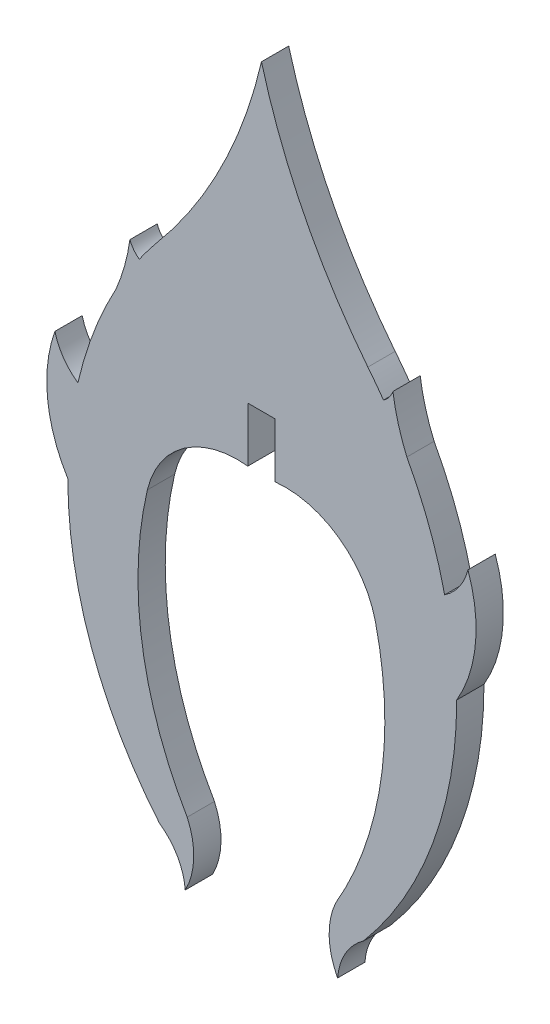
SolidWorks part; units mm, degrees
ref_plane "Front Plane" through (0, 0, 0) normal (0, 0, 1) x (1, 0, 0)
ref_plane "Top Plane" through (0, 0, 0) normal (0, 1, 0) x (1, 0, 0)
ref_plane "Right Plane" through (0, 0, 0) normal (1, 0, 0) x (0, 0, -1)
sketch "Sketch1" plane through (0, 0, 0) normal (0, 0, 1) x (1, 0, 0)
  line L0 (-0.0002, 4.1528) -> (-0.0002, -21.0581) construction
  line L1 (-0.7628, 4.1517) -> (0.7632, 4.1527)
  line L2 (0.7632, 4.1527) -> (0.7632, 1.1018)
  line L3 (-0.7629, 1.1001) -> (-0.7628, 4.1517)
  arc A0 (5.9496, 9.2509) -> (0.0014, 21.0581) centre (31.9942, 29.7732) cw
  arc A1 (0.0014, 21.0581) -> (-5.8741, 9.3403) centre (-27.1517, 27.3412) cw
  arc A2 (10.241, 0.37) -> (11.5437, 2.2352) centre (8.4439, 3.0127) ccw
  arc A3 (10.241, 0.37) -> (8.1293, 5.9869) centre (-11.0731, -4.4378) ccw
  arc A4 (-10.8209, -4.5371) -> (-11.5437, 2.2357) centre (-4.1437, -0.3996) cw
  arc A5 (-10.2597, 0.3834) -> (-11.5437, 2.2357) centre (-8.4439, 3.0132) cw
  arc A6 (-10.8209, -4.5371) -> (-5.6952, -18.6609) centre (11.1596, -4.5521) ccw
  arc A7 (8.1293, 5.9869) -> (7.3502, 8.7721) centre (18.1454, 10.2899) cw
  arc A8 (7.3502, 8.7721) -> (6.8224, 8.0883) centre (6.0438, 9.2348) cw
  arc A9 (6.8224, 8.0883) -> (5.9496, 9.2509) centre (-11.0731, -4.4378) ccw
  arc A10 (-7.3506, 8.7721) -> (-6.8228, 8.0883) centre (-6.0442, 9.2348) ccw
  arc A11 (-8.1296, 5.9869) -> (-7.3506, 8.7721) centre (-18.1457, 10.2899) ccw
  arc A12 (-8.1296, 5.9869) -> (-10.2597, 0.3834) centre (11.1596, -4.5521) ccw
  arc A13 (6.3714, -2.8593) -> (0.7632, 1.1018) centre (1.3367, -4.037) ccw
  arc A14 (4.1511, -17.5864) -> (6.3714, -2.8593) centre (-13.2425, -7.4332) ccw
  arc A15 (-4.2589, -21.1681) -> (-5.6952, -18.6609) centre (-7.6291, -21.4338) ccw
  arc A16 (5.6949, -18.6609) -> (10.9146, -4.3826) centre (-11.0731, -4.4378) ccw
  arc A17 (-5.8741, 9.3403) -> (-6.8228, 8.0883) centre (11.1596, -4.5521) ccw
  arc A19 (-6.3754, -2.8562) -> (-4.1515, -17.5864) centre (13.2385, -7.4279) ccw
  arc A20 (-0.7629, 1.1001) -> (-6.3754, -2.8562) centre (-1.3417, -4.038) ccw
  arc A21 (10.9146, -4.3826) -> (11.5437, 2.2352) centre (4.1437, -0.4002) ccw
  arc A22 (4.1511, -17.5864) -> (4.2585, -21.1681) centre (7.8177, -19.2689) ccw
  arc A23 (4.2585, -21.1681) -> (5.6949, -18.6609) centre (7.6287, -21.4338) cw
  arc A24 (-4.1515, -17.5864) -> (-4.2589, -21.1681) centre (-7.8181, -19.2689) cw
extrude "Boss-Extrude1" add sketch "Sketch1" along normal blind 1.524
